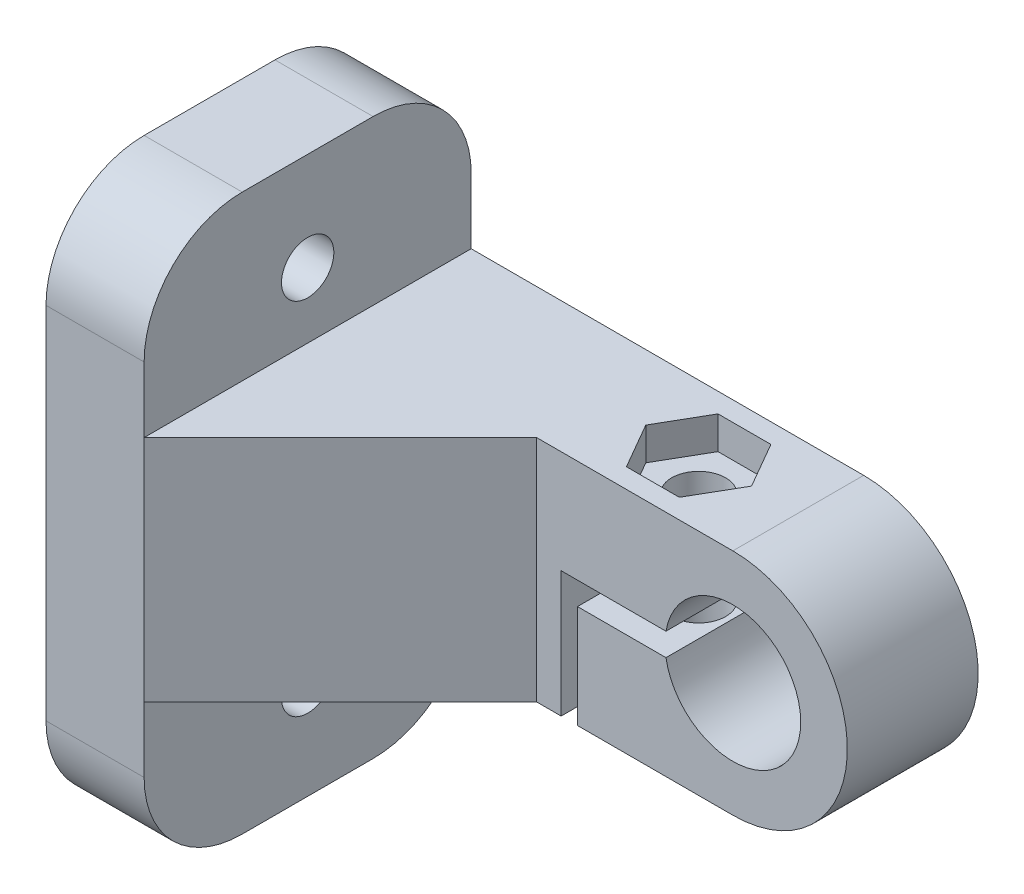
SolidWorks part; units mm, degrees
ref_plane "Plano frontal" through (0, 0, 0) normal (0, 0, 1) x (1, 0, 0)
ref_plane "Plano superior" through (0, 0, 0) normal (0, 1, 0) x (1, 0, 0)
ref_plane "Plano direito" through (0, 0, 0) normal (1, 0, 0) x (0, 0, -1)
sketch "Esboço2" plane through (0, 0, 0) normal (0, 0, 1) x (1, 0, 0)
  line L0 (0, 7) -> (-24, 7)
  line L1 (-30, 17) -> (-30, -17)
  line L2 (-24, -7) -> (-10.5, -7)
  line L3 (-4, 0) -> (-10, 0) construction
  line L4 (-10, 0) -> (-10, -7) construction
  line L5 (-4.0905, 0.7) -> (-10.5, 0.7)
  line L6 (-10.5, 0.7) -> (-10.5, -7)
  line L7 (-4.0905, -0.7) -> (-9.5, -0.7)
  line L8 (-9.5, -0.7) -> (-9.5, -7)
  line L9 (-24, 7) -> (-24, 17)
  line L10 (-24, 17) -> (-30, 17)
  line L11 (-9.5, -7) -> (0, -7)
  line L12 (-24, -7) -> (-24, -17)
  line L13 (-24, -17) -> (-30, -17)
  arc A0 (-4.0905, -0.7) -> (-4.0905, 0.7) centre (0, 0) ccw
  arc A1 (0, -7) -> (0, 7) centre (0, 0) ccw
  point P5 (-30, 0)
  dimension "D1" = 8.3
  dimension "D3" = 7
  dimension "D8" = 6
  dimension "D2" = 10
  dimension "D6" = 20
  dimension "D7" = 10
  dimension "D4" = 0.7
  dimension "D5" = 0.7
  dimension "D9" = 1
extrude "Ressalto-extrusão1" add sketch "Esboço2" along normal blind 20
sketch "Esboço4" plane through (-30, 0, 0) normal (-1, 0, 0) x (0, 0, 1)
  line L2 (20, 17) -> (0, 17) construction
  line L3 (0, 0) -> (20, 0) construction
  line L4 (0, 17) -> (0, -17) construction
  line L5 (20, 17) -> (20, -17) construction
  circle A0 centre (10, 11) radius 1.6
  circle A1 centre (10, -11) radius 1.6
  point P8 (10, 17)
  dimension "D2" = 3.2
  dimension "D1" = 6
extrude "Corte-extrusão2" cut sketch "Esboço4" against normal blind 18
sketch "Esboço5" plane through (-30, 0, 0) normal (-1, 0, 0) x (0, 0, 1)
  circle A0 centre (10, 11) radius 5.25
  circle A1 centre (10, -11) radius 5.25
  dimension "D1" = 10.5
extrude "Corte-extrusão3" cut sketch "Esboço5" against normal blind 1
fillet "Filete1" radius 6 4 edges at (-27, -17, 20) (-27, -17, 0) (-27, 17, 20) (-27, 17, 0)
sketch "Esboço8" plane through (0, 7, 0) normal (0, 1, 0) x (1, 0, 0)
  line L0 (-24, -20) -> (-12, -8)
  line L1 (-12, -8) -> (7, -8)
  line L2 (7, -20) -> (7, 0) construction
  line L3 (7, -8) -> (7, -20)
  line L4 (0, -20) -> (7, -20) construction
  line L5 (7, -20) -> (-24, -20)
  dimension "D1" = 12
  dimension "D2" = 45
extrude "Corte-extrusão6" cut sketch "Esboço8" against normal through all
sketch "Esboço6" plane through (0, 0.7, 0) normal (0, -1, 0) x (1, 0, 0)
  line L0 (-4.0905, 8) -> (-4.0905, 0) construction
  line L1 (7, 0) -> (7, 8) construction
  circle A0 centre (-6.0905, 4) radius 1.65
  point P13 (7, 4)
  dimension "D1" = 3.3
  dimension "D2" = 2
extrude "Corte-extrusão4" cut sketch "Esboço6" against normal through all both and the other way through all
sketch "Esboço7" plane through (0, 7, 0) normal (0, 1, 0) x (1, 0, 0)
  line L1 (-2.8574, -4) -> (-4.474, -1.2)
  line L2 (-4.474, -1.2) -> (-7.7071, -1.2)
  line L3 (-7.7071, -1.2) -> (-9.3237, -4)
  line L4 (-9.3237, -4) -> (-7.7071, -6.8)
  line L5 (-7.7071, -6.8) -> (-4.474, -6.8)
  line L6 (-4.474, -6.8) -> (-2.8574, -4)
  circle A0 centre (-6.0905, -4) radius 2.8 construction
  dimension "D1" = 5.6
extrude "Corte-extrusão5" cut sketch "Esboço7" against normal blind 2
